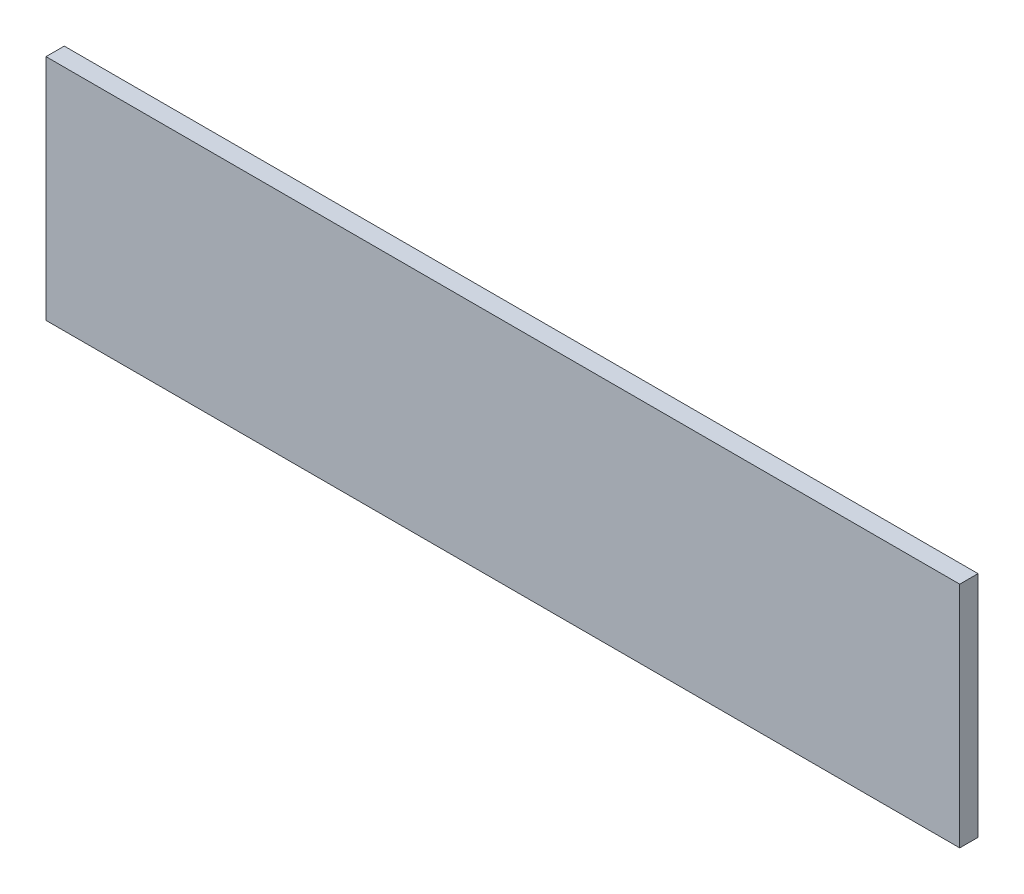
SolidWorks part; units mm, degrees
ref_plane "Front Plane" through (0, 0, 0) normal (0, 0, 1) x (1, 0, 0)
ref_plane "Top Plane" through (0, 0, 0) normal (0, 1, 0) x (1, 0, 0)
ref_plane "Right Plane" through (0, 0, 0) normal (1, 0, 0) x (0, 0, -1)
sketch "Sketch1" plane through (0, 0, 0) normal (0, 0, 1) x (1, 0, 0)
  line L1 (-500, -125) -> (500, -125)
  line L2 (-500, -125) -> (-500, 125)
  line L3 (-500, 125) -> (500, 125)
  line L4 (500, -125) -> (500, 125)
  line L5 (-500, -125) -> (500, 125) construction
  line L6 (-500, 125) -> (500, -125) construction
  point P0 (0, 0)
  dimension "D1" = 250
  dimension "D2" = 1000
extrude "Boss-Extrude1" add sketch "Sketch1" along normal blind 20
